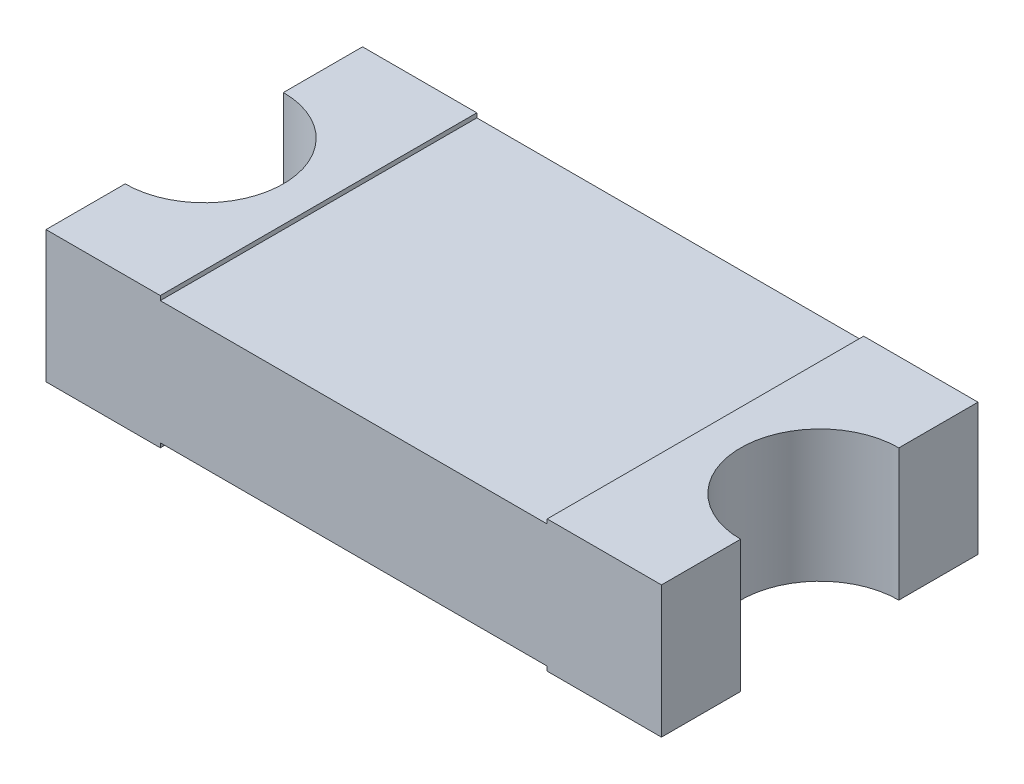
SolidWorks part; units mm, degrees
ref_plane "Front Plane" through (0, 0, 0) normal (0, 0, 1) x (1, 0, 0)
ref_plane "Top Plane" through (0, 0, 0) normal (0, 1, 0) x (1, 0, 0)
ref_plane "Right Plane" through (0, 0, 0) normal (1, 0, 0) x (0, 0, -1)
sketch "Sketch1" plane through (0, 0, 0) normal (0, 1, 0) x (1, 0, 0)
  line L0 (1.75, 0.45) -> (1.75, 0.9)
  line L1 (-1.75, -0.9) -> (1.75, -0.9)
  line L3 (-1.75, 0.9) -> (1.75, 0.9)
  line L4 (1.75, -0.9) -> (1.75, -0.45)
  line L5 (-1.75, -0.9) -> (1.75, 0.9) construction
  line L6 (-1.75, 0.9) -> (1.75, -0.9) construction
  line L7 (1.75, 0.9) -> (1.75, -0.9) construction
  line L8 (0, 0.9) -> (0, -0.9) construction
  line L9 (-1.75, -0.9) -> (-1.75, -0.45)
  line L10 (-1.75, 0.45) -> (-1.75, 0.9)
  arc A0 (1.75, 0.45) -> (1.75, -0.45) centre (1.75, 0) ccw
  arc A1 (-1.75, 0.45) -> (-1.75, -0.45) centre (-1.75, 0) cw
  point P0 (0, 0)
  point P9 (1.75, 0)
  dimension "D3" = 0.45
  dimension "D1" = 3.5
  dimension "D2" = 1.8
extrude "Boss-Extrude1" add sketch "Sketch1" along normal blind 0.75
sketch "Sketch2" plane through (0, 0.75, 0) normal (0, 1, 0) x (1, 0, 0)
  line L0 (-1.75, -0.9) -> (1.75, 0.9) construction
  line L1 (1.75, -0.9) -> (-1.75, 0.9) construction
  line L2 (1.75, 0.9) -> (-1.75, 0.9) construction
  line L3 (-1.1, 0.9) -> (1.1, 0.9)
  line L4 (-1.1, 0.9) -> (-1.1, -0.9)
  line L5 (-1.1, -0.9) -> (1.1, -0.9)
  line L6 (1.1, 0.9) -> (1.1, -0.9)
  line L7 (-1.1, 0.9) -> (1.1, -0.9) construction
  line L8 (-1.1, -0.9) -> (1.1, 0.9) construction
  arc A0 (-1.75, -0.45) -> (-1.75, 0.45) centre (-1.75, 0) ccw construction
  point P8 (0, 0)
  point P13 (-1.3, 0)
  dimension "D1" = 0.2
extrude "Cut-Extrude1" cut sketch "Sketch2" against normal blind 0.025
ref_plane "Plane1" through (0, 0.375, 0) normal (0, 1, 0) x (1, 0, 0)
mirror "Mirror1" about plane through (0, 0.375, 0) normal (0, 1, 0) of "Cut-Extrude1"
